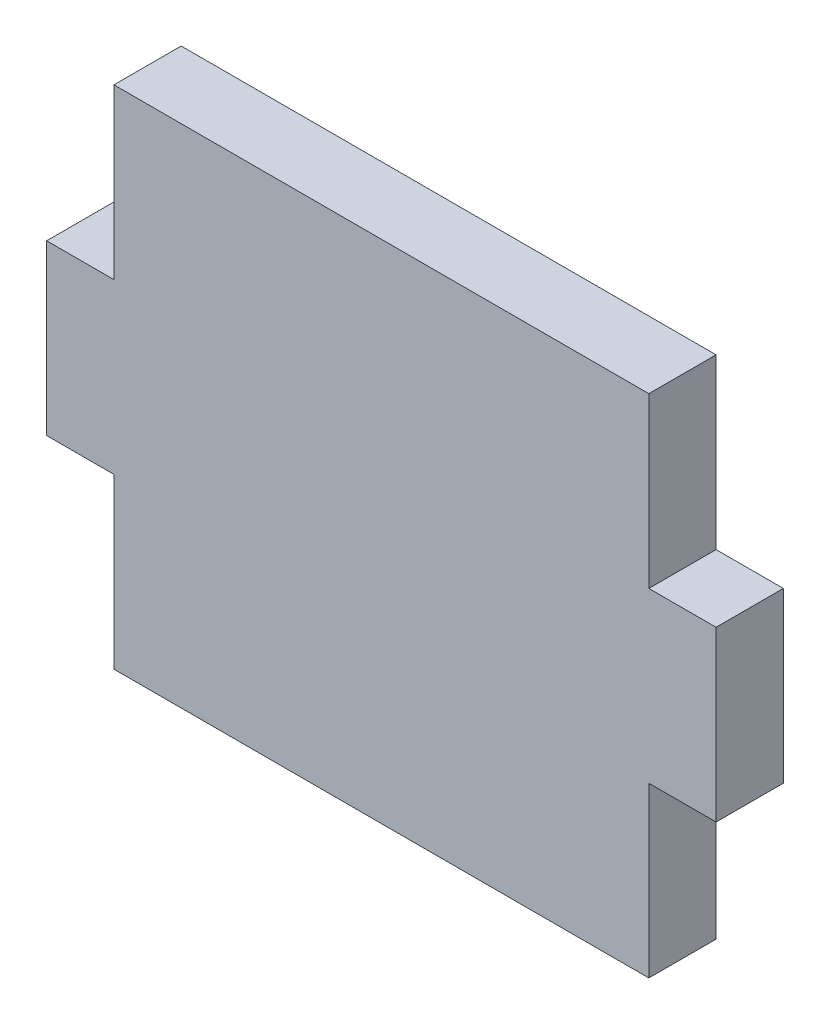
SolidWorks part; units mm, degrees
ref_plane "Front Plane" through (0, 0, 0) normal (0, 0, 1) x (1, 0, 0)
ref_plane "Top Plane" through (0, 0, 0) normal (0, 1, 0) x (1, 0, 0)
ref_plane "Right Plane" through (0, 0, 0) normal (1, 0, 0) x (0, 0, -1)
sketch "Sketch1" plane through (0, 0, 0) normal (0, 0, 1) x (1, 0, 0)
  line L1 (0, 0) -> (53.086, 0)
  line L2 (0, 0) -> (0, 40.132)
  line L3 (0, 40.132) -> (53.086, 40.132)
  line L4 (53.086, 0) -> (53.086, 40.132)
  dimension "D1" = 53.086
  dimension "D2" = 40.132
extrude "Boss-Extrude1" add sketch "Sketch1" along normal blind 5.334
sketch "Sketch6" plane through (0, 0, 5.334) normal (0, 0, 1) x (1, 0, 0)
  line L0 (0, 20.066) -> (53.086, 20.066) construction
  line L1 (0, 40.132) -> (5.334, 40.132)
  line L2 (0, 40.132) -> (0, 26.7547)
  line L3 (0, 26.7547) -> (5.334, 26.7547)
  line L4 (5.334, 40.132) -> (5.334, 26.7547)
  line L5 (0, 40.132) -> (0, 0) construction
  line L6 (53.086, 0) -> (53.086, 40.132) construction
  line L7 (26.543, 40.132) -> (26.543, 0) construction
  line L8 (53.086, 40.132) -> (0, 40.132) construction
  line L9 (0, 0) -> (53.086, 0) construction
  line L10 (0, 13.3773) -> (5.334, 13.3773)
  line L11 (5.334, 0) -> (5.334, 13.3773)
  line L12 (0, 0) -> (5.334, 0)
  line L13 (0, 0) -> (0, 13.3773)
  line L14 (53.086, 0) -> (53.086, 13.3773)
  line L15 (53.086, 0) -> (47.752, 0)
  line L16 (47.752, 0) -> (47.752, 13.3773)
  line L17 (53.086, 13.3773) -> (47.752, 13.3773)
  line L18 (53.086, 26.7547) -> (47.752, 26.7547)
  line L19 (47.752, 40.132) -> (47.752, 26.7547)
  line L20 (53.086, 40.132) -> (47.752, 40.132)
  line L21 (53.086, 40.132) -> (53.086, 26.7547)
  dimension "D1" = 5.334
  dimension "D2" = 13.3773
extrude "Cut-Extrude2" cut sketch "Sketch6" against normal through all contours L2 L1 L4 L3 | L18 L19 L20 L21 | L14 L17 L16 L15 | L10 L11 L12 L13
equation "\"GMaterial\" = 0.21in"
equation "\"MDF\"= 0.21in"
equation "\"Foamcore\"= 0.2in"
equation "\"D2@Sketch1\"=\"GMaterial\"+1.37"
equation "\"D1@Sketch1\"=\"GMaterial\"*2 + 1.67"
equation "\"D1@Boss-Extrude1\"=\"GMaterial\""
equation "\"D1@Sketch6\"=\"GMaterial\""
equation "\"D2@Sketch6\"=(\"GMaterial\"+1.37)/3"
